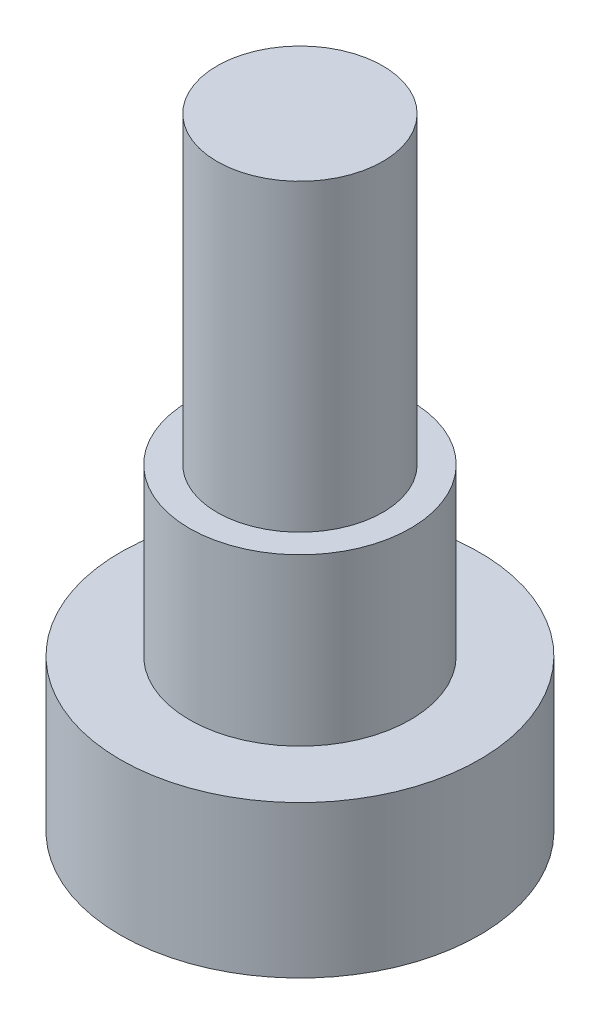
SolidWorks part; units mm, degrees
ref_plane "前视基准面" through (0, 0, 0) normal (0, 0, 1) x (1, 0, 0)
ref_plane "上视基准面" through (0, 0, 0) normal (0, 1, 0) x (1, 0, 0)
ref_plane "右视基准面" through (0, 0, 0) normal (1, 0, 0) x (0, 0, -1)
sketch "草图1" plane through (0, 0, 0) normal (0, 1, 0) x (1, 0, 0)
  circle A0 centre (0, 0) radius 6.5
extrude "凸台-拉伸1" add sketch "草图1" along normal blind 5.5
sketch "草图2" plane through (0, 5.5, 0) normal (0, 1, 0) x (1, 0, 0)
  circle A0 centre (0, 0) radius 4
extrude "凸台-拉伸2" add sketch "草图2" along normal blind 6 contours A0
sketch "草图3" plane through (0, 11.5, 0) normal (0, 1, 0) x (1, 0, 0)
  circle A0 centre (0, 0) radius 3
extrude "凸台-拉伸3" add sketch "草图3" along normal blind 11 contours A0
